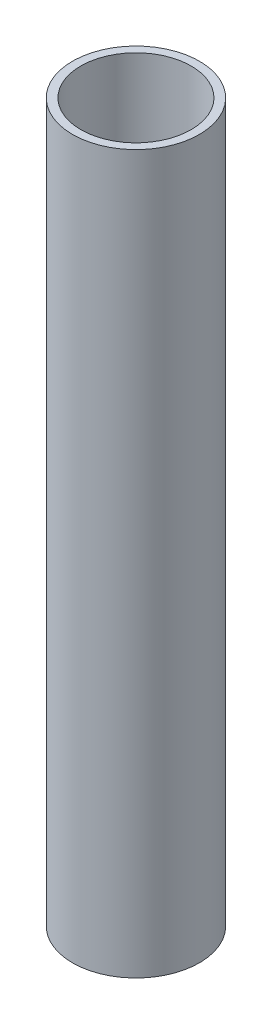
SolidWorks part; units mm, degrees
ref_plane "前基準面" through (0, 0, 0) normal (0, 0, 1) x (1, 0, 0)
ref_plane "上基準面" through (0, 0, 0) normal (0, 1, 0) x (1, 0, 0)
ref_plane "右基準面" through (0, 0, 0) normal (1, 0, 0) x (0, 0, -1)
sketch "草圖1" plane through (0, 0, 0) normal (0, 1, 0) x (1, 0, 0)
  circle A0 centre (0, 0) radius 20
  circle A1 centre (0, 0) radius 23
  dimension "D1" = 40
  dimension "D2" = 46
extrude "填料-伸長1" add sketch "草圖1" along normal blind 260
